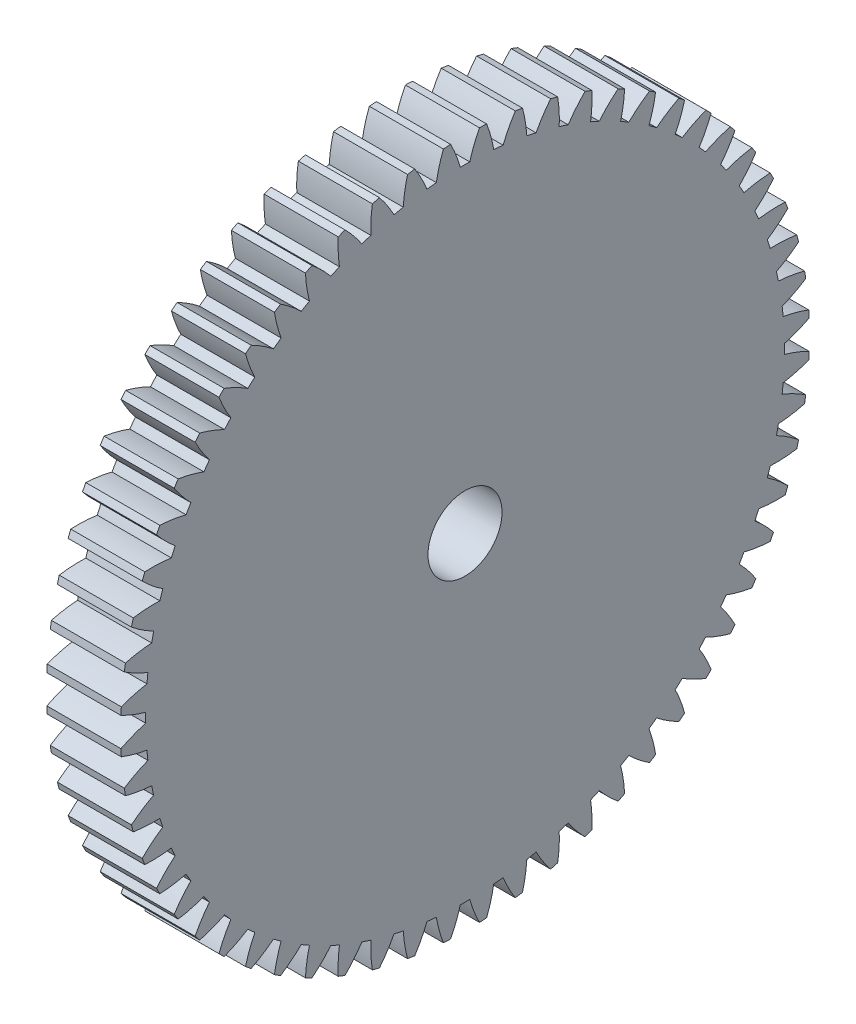
SolidWorks part; units mm, degrees
ref_plane "Plane1" through (0, 0, 0) normal (0, 0, 1) x (1, 0, 0)
ref_plane "Plane2" through (0, 0, 0) normal (0, 1, 0) x (1, 0, 0)
ref_plane "Plane3" through (0, 0, 0) normal (1, 0, 0) x (0, 0, -1)
other "Configuration Table"
sketch "HoldingSke" plane through (0, 0, 0) normal (0, 1, 0) x (1, 0, 0)
  line L0 (0, 0) -> (0.3333, -0.5774)
  line L1 (-15, 0) -> (100, 0) construction
  line L2 (0, 0) -> (-2.1039, 2.3779)
  line L3 (0, 0) -> (-11.863, 4.5341)
  line L4 (0, 0) -> (4.318, 7.479)
  line L5 (0, 0) -> (-46.8476, -17.4728)
  line L6 (0, 0) -> (-8.2896, -5.593)
  line L7 (-2.1039, 2.3779) -> (8.6586, 51.2059)
  line L8 (-76.2, 54.61) -> (-74.4, 54.61)
  line L9 (-71.009, 38.7566) -> (-53.1078, 45.2721)
  line L10 (-76.2, 71.12) -> (104.1128, 71.12)
  line L11 (0, 0) -> (-10, 0)
  line L12 (-76.2, 101.6) -> (-76.147, 101.6)
  line L13 (24.9733, 27.94) -> (52.9518, 28.4284)
  line L14 (24.9733, 27.94) -> (24.9743, 27.94)
  line L15 (24.9733, 27.94) -> (100.4006, 29.5858)
  line L16 (-63.627, -1.5) -> (-12.827, -1.5)
  circle A0 centre (0, 0) radius 5
  circle A1 centre (0, 0) radius 37.5
  circle A2 centre (0, 0) radius 37.5
  circle A3 centre (0, 0) radius 5
  dimension "MHD" = 75
  dimension "Hub_dia" = 75
  dimension "Bore" = 10
  dimension "MBD" = 10
  dimension "Num_teeth" = 60
  dimension "Pitch" = 0.6667
  dimension "Overall_len" = 50
  dimension "Show_teeth" = 60
  dimension "Thickness" = 10
  dimension "OAL" = 50.0001
  dimension "T_dim" = 1.8
  dimension "Ap" = 20
  dimension "H" = 19.05
  dimension "Pitch_radius" = 180.3128
  dimension "Width" = 10
  dimension "Backlash" = 0.053
  dimension "Addendum_fac" = 1
  dimension "Dedendum_fac" = 1.25
  dimension "Clearance_fac" = 0.25
  dimension "Dedendum_add" = 0.001
  dimension "Module" = 1.5
sketch "BasProSke" plane through (0, 0, 0) normal (0, 1, 0) x (1, 0, 0)
  line L0 (-10, 0) -> (60, 0) construction
  line L1 (0, 0) -> (0, 46.5)
  line L2 (0, 0) -> (10, 0)
  line L3 (10, 0) -> (10, 46.5)
  line L4 (10, 46.5) -> (0, 46.5)
  dimension "Thickness" = 10
  dimension "Diameter" = 93
revolve "Base-Revolve" add sketch "BasProSke" angle 360 about L0
sketch "TooCutSke" plane through (0, 0, 0) normal (1, 0, 0) x (0, 0, -1)
  line L1 (0, 0) -> (0, 107) construction
  line L2 (0, 0) -> (-1.2707, 44.9821) construction
  line L3 (0, 0) -> (-4.7089, 89.8505) construction
  line L4 (-1.2707, 44.9821) -> (-2.3544, 44.9253) construction
  arc A0 (0.6387, 43.1193) -> (-0.6387, 43.1193) centre (0, 0) ccw
  arc A1 (1.9554, 46.4843) -> (-1.9554, 46.4843) centre (0, 0) ccw
  circle A2 centre (0, 0) radius 45 construction
  circle A3 centre (0, 0) radius 42.2862 construction
  arc A4 (-0.6387, 43.1193) -> (-1.9554, 46.4843) centre (-17.9747, 38.2757) ccw
  arc A5 (1.9554, 46.4843) -> (0.6387, 43.1193) centre (17.9747, 38.2757) ccw
  dimension "Root_dia" = 86.248
  dimension "Overcut_dia" = 93.0508
  dimension "Pitch_dia" = 90
  dimension "Base_dia" = 84.5723
  dimension "Flank_rad" = 18
  dimension "Half_ang" = 3
  dimension "Half_CT" = 1.0852
extrude "ToothCut" cut sketch "TooCutSke" along normal through all
fillet "Breaks" [suppressed] radius 0.03
fillet "RootFillets" [suppressed] radius 0.376
pattern_circular "TeethCuts" count 60 every 6 about axis through (-10, 0, 0) along (1, 0, 0) of "ToothCut", "RootFillets", "Breaks"
sketch "HubNeaOneSke" plane through (0, 0, 0) normal (-1, 0, 0) x (0, 0, 1)
  circle A0 centre (0, 0) radius 37.5
  dimension "Diameter" = 75
extrude "HubNearOne" [suppressed] add sketch "HubNeaOneSke" along normal blind 40.0001
sketch "HubNeaBotSke" plane through (0, 0, 0) normal (-1, 0, 0) x (0, 0, 1)
  circle A0 centre (0, 0) radius 37.5
  dimension "Diameter" = 75
extrude "HubNearBoth" [suppressed] add sketch "HubNeaBotSke" along normal blind 20
ref_plane "FarPln" through (10, 0, 0) normal (1, 0, 0) x (0, 0, -1)
sketch "HubFarSke" plane through (10, 0, 0) normal (1, 0, 0) x (0, 0, -1)
  circle A0 centre (0, 0) radius 37.5
  dimension "Diameter" = 75
extrude "HubFar" [suppressed] add sketch "HubFarSke" along normal blind 20
sketch "BorSke" plane through (0, 0, 0) normal (1, 0, 0) x (0, 0, -1)
  circle A0 centre (0, 0) radius 5
  dimension "Diameter" = 10
extrude "Bore" cut sketch "BorSke" along normal mid plane 100.0001
sketch "KeySke" plane through (0, 0, 0) normal (1, 0, 0) x (0, 0, -1)
  line L0 (-2, 0) -> (-2, 6.8)
  line L1 (-2, 6.8) -> (2, 6.8)
  line L2 (2, 6.8) -> (2, 0)
  line L3 (0, 0) -> (0, 34) construction
  line L4 (-2, 0) -> (2, 0)
  dimension "Offset" = 6.8
  dimension "Width" = 4
extrude "Keyway" [suppressed] cut sketch "KeySke" along normal mid plane 100.0001
pattern_circular "Keyway2" [suppressed] count 2 every 90 about axis through (-10, 0, 0) along (1, 0, 0)
equation "' \"Module@HoldingSke\" = 6.35"
equation "' \"Num_teeth@HoldingSke\" = 12"
equation "' \"Ap@HoldingSke\" =  20"
equation "' \"Ap@HoldingSke\" = 20"
equation "' \"Width@HoldingSke\" = 0.5 * 25.4"
equation "' \"Hub_dia@HoldingSke\"= 1 * 25.4"
equation "' \"Hub_dia@HoldingSke\" = 1 * 25.4"
equation "' \"Overall_len@HoldingSke\" = 1.0 * 25.4"
equation "' \"Bore@HoldingSke\" = 0.75 * 25.4"
equation "' \"T_dim@HoldingSke\" = 0.1 * 25.4"
equation "' \"Width@KeySke\" = 0.25 * 25.4"
equation "' \"Show_teeth@HoldingSke\" = 13"
equation "' \"Backlash@HoldingSke\" = 0.009 * 25.4"
equation "' \"Addendum_fac@HoldingSke\" = 1.0"
equation "' \"Dedendum_fac@HoldingSke\" = 1.25"
equation "' \"Dedendum_add@HoldingSke\" = 0.00005 * 25.4"
equation "' \"Clearance_fac@HoldingSke\" = 0.25"
equation "\"Pitch@HoldingSke\" = 1 / \"Module@HoldingSke\""
equation "\"Overcut_dia@TooCutSke\" = (\"Num_teeth@HoldingSke\" + 2 * \"Addendum_fac@HoldingSke\") / \"Pitch@HoldingSke\" + 0.002 * 25.4"
equation "\"Pitch_dia@TooCutSke\" = \"Num_teeth@HoldingSke\" / \"Pitch@HoldingSke\""
equation "\"Base_dia@TooCutSke\" = \"Num_teeth@HoldingSke\" / \"Pitch@HoldingSke\" * cos((\"Ap@HoldingSke\"  * 3.14159265 / 180))"
equation "\"Root_dia@TooCutSke\" = (\"Num_teeth@HoldingSke\" + 2) / \"Pitch@HoldingSke\" - 2 * (\"Addendum_fac@HoldingSke\" + \"Dedendum_fac@HoldingSke\") / \"Pitch@HoldingSke\" - \"Dedendum_add@HoldingSke\" * 2"
equation "\"Half_ang@TooCutSke\" = 180 / \"Num_teeth@HoldingSke\""
equation "\"Half_CT@TooCutSke\" = \"Num_teeth@HoldingSke\" / \"Pitch@HoldingSke\" * sin((3.14159265 / 2 / \"Num_teeth@HoldingSke\")) / 2 - 7 * \"Backlash@HoldingSke\" / 4"
equation "\"Flank_rad@TooCutSke\" = \"Num_teeth@HoldingSke\" / \"Pitch@HoldingSke\" / 5"
equation "\"Radius@RootFillets\" = \"Clearance_fac@HoldingSke\" / \"Pitch@HoldingSke\" + \"Dedendum_add@HoldingSke\""
equation "\"Break_rad@Breaks\" = 0.02 / \"Pitch@HoldingSke\""
equation "\"Thickness@HoldingSke\" = \"Width@HoldingSke\""
equation "\"OAL@HoldingSke\" = \"Thickness@HoldingSke\""
equation "\"MHD@HoldingSke\" = (\"Num_teeth@HoldingSke\" + 2) / \"Pitch@HoldingSke\" - 2 * (\"Addendum_fac@HoldingSke\" + \"Dedendum_fac@HoldingSke\")  / \"Pitch@HoldingSke\" - \"Dedendum_add@HoldingSke\" * 2"
equation "\"MBD@HoldingSke\" = (\"Num_teeth@HoldingSke\" + 2) / \"Pitch@HoldingSke\" - 2 * (\"Addendum_fac@HoldingSke\" + \"Dedendum_fac@HoldingSke\")  / \"Pitch@HoldingSke\" - \"Dedendum_add@HoldingSke\" * 2 - 0.002 * 25.4"
equation "\"MHD@HoldingSke\" = ((sgn( \"MHD@HoldingSke\" - \"Hub_dia@HoldingSke\" )-1)*( \"MHD@HoldingSke\" - \"Hub_dia@HoldingSke\" ))/-2+ \"Hub_dia@HoldingSke\""
equation "\"MBD@HoldingSke\" = ((sgn( \"MBD@HoldingSke\" - \"Bore@HoldingSke\" )-1)*( \"MBD@HoldingSke\" - \"Bore@HoldingSke\" ))/-2+ \"Bore@HoldingSke\""
equation "\"OAL@HoldingSke\" = ((sgn( \"OAL@HoldingSke\" - \"Overall_len@HoldingSke\" )+1)*( \"OAL@HoldingSke\" - \"Overall_len@HoldingSke\" ))/2 + \"Overall_len@HoldingSke\" + 0.000002 * 25.4"
equation "\"Num_teeth@TeethCuts\" = int( \"Show_teeth@HoldingSke\" ) + 1"
equation "\"Num_teeth@TeethCuts\" = ((sgn( \"Num_teeth@TeethCuts\" - \"Num_teeth@HoldingSke\" )-1)*( \"Num_teeth@TeethCuts\" - \"Num_teeth@HoldingSke\" ))/-2+ \"Num_teeth@HoldingSke\""
equation "\"Num_teeth@TeethCuts\" = ((sgn( \"Num_teeth@TeethCuts\" - 2.0)+1)*( \"Num_teeth@TeethCuts\" - 2.0))/2 +2.0"
equation "\"Angle@TeethCuts\" = 360.0 / \"Num_teeth@HoldingSke\""
equation "\"Diameter@BasProSke\" = (\"Num_teeth@HoldingSke\" + 2 * \"Addendum_fac@HoldingSke\") / \"Pitch@HoldingSke\""
equation "\"Thickness@BasProSke\"  = \"Thickness@HoldingSke\""
equation "' \"Fillet_rad@BasProSke\" =  \"Thickness@HoldingSke\" * 0.05"
equation "' \"Fillet_rad@BasProSke\" = \"Thickness@HoldingSke\" * 0.05"
equation "\"MHD@HoldingSke\" = ((sgn( \"MHD@HoldingSke\" - \"Root_dia@TooCutSke\" )-1)*( \"MHD@HoldingSke\" - \"Root_dia@TooCutSke\" ))/-2+ \"Root_dia@TooCutSke\""
equation "\"Diameter@HubNeaOneSke\" = \"MHD@HoldingSke\""
equation "\"Length@HubNearOne\" = \"OAL@HoldingSke\" - \"Thickness@BasProSke\""
equation "\"Diameter@HubNeaBotSke\" = \"MHD@HoldingSke\""
equation "\"Length@HubNearBoth\" = ( \"OAL@HoldingSke\" - \"Thickness@BasProSke\" ) / 2.0"
equation "\"Thickness@FarPln\" = \"Thickness@BasProSke\""
equation "\"Diameter@HubFarSke\" = \"MHD@HoldingSke\""
equation "\"Length@HubFar\" = ( \"OAL@HoldingSke\" - \"Thickness@BasProSke\" ) / 2.0"
equation "\"Diameter@BorSke\" = \"MBD@HoldingSke\""
equation "\"D1@Bore\" = \"OAL@HoldingSke\" * 2.0"
equation "\"D1@Keyway\" = \"OAL@HoldingSke\" * 2.0"
equation "\"Offset@KeySke\" = \"T_dim@HoldingSke\" + \"MBD@HoldingSke\" / 2.0"
